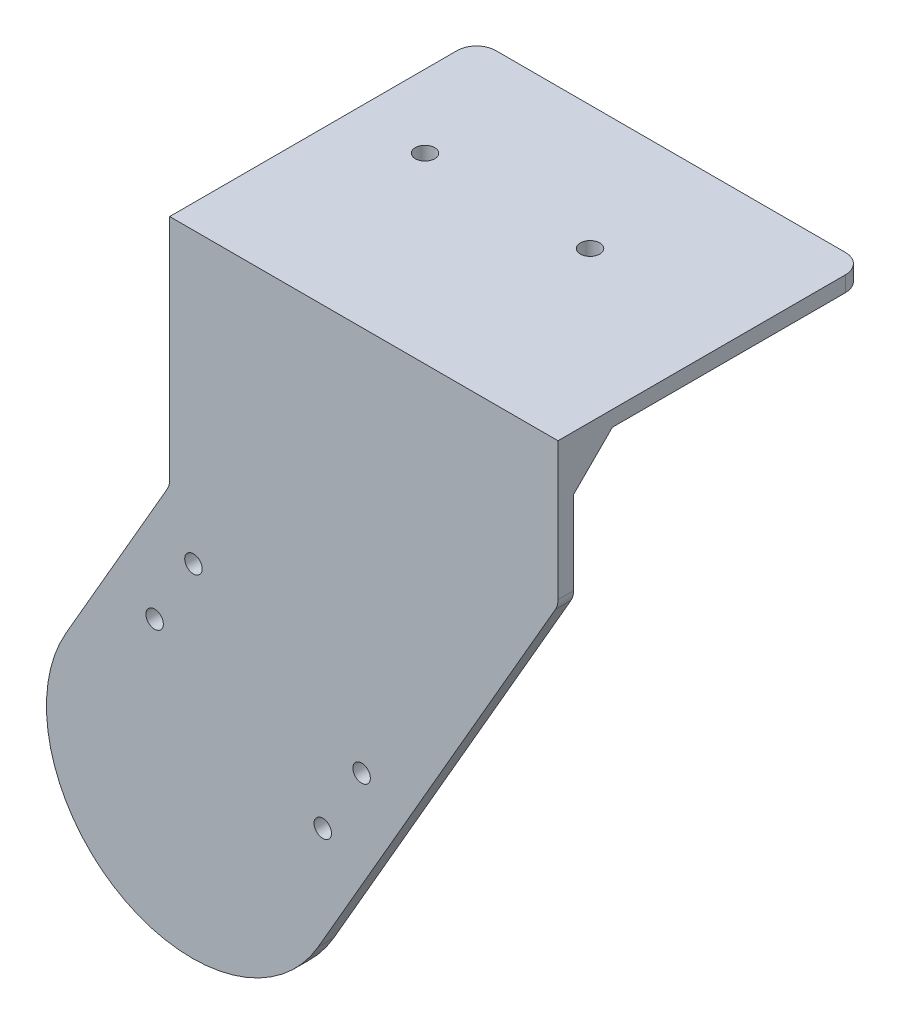
SolidWorks part; units mm, degrees
ref_plane "Front Plane" through (0, 0, 0) normal (0, 0, 1) x (1, 0, 0)
ref_plane "Top Plane" through (0, 0, 0) normal (0, 1, 0) x (1, 0, 0)
ref_plane "Right Plane" through (0, 0, 0) normal (1, 0, 0) x (0, 0, -1)
sketch "Sketch1" plane through (0, 0, 0) normal (0, 0, 1) x (1, 0, 0)
  line L0 (0, 0) -> (40.2373, 0) construction
  line L1 (64.9519, -37.5) -> (0, 0) construction
  line L2 (0, 0) -> (-64.9519, 37.5) construction
  line L3 (-64.9519, 37.5) -> (-11.547, 130)
  line L4 (64.9519, -37.5) -> (188.453, 176.4102)
  line L5 (-11.547, 130) -> (-11.547, 250)
  line L6 (-11.547, 250) -> (188.453, 250)
  line L7 (188.453, 250) -> (188.453, 176.4102)
  arc A0 (64.9519, -37.5) -> (-64.9519, 37.5) centre (0, 0) cw
  dimension "D2" = 75
  dimension "D1" = 30
  dimension "D4" = 130
  dimension "D5" = 200
  dimension "D6" = 120
extrude "Boss-Extrude1" add sketch "Sketch1" along normal blind 8
sketch "Sketch4" plane through (-11.547, 0, 0) normal (-1, 0, 0) x (0, 0, 1)
  line L5 (0, 242) -> (0, 250)
  line L6 (0, 250) -> (0, 130) construction
  line L7 (0, 250) -> (-150, 250)
  line L8 (0, 250) -> (0, 130)
  line L9 (0, 130) -> (8, 130)
  line L10 (8, 130) -> (8, 250)
  line L11 (8, 250) -> (0, 250)
  line L13 (0, 130) -> (8, 130)
  line L15 (-150, 250) -> (-150, 242)
  line L16 (-150, 242) -> (0, 242)
  dimension "D4" = 150
  dimension "D5" = 8
  dimension "D3" = 0
extrude "Boss-Extrude2" add sketch "Sketch4" along direction (-1, 0, 0) on the side against the normal up to surface (200 mm away)
chamfer "Chamfer1" distance 20 angle 45 1 edges at (88.453, 242, 0)
sketch "Sketch5" plane through (0, 250, 0) normal (0, 1, 0) x (1, 0, 0)
  line L0 (188.453, -8) -> (188.453, 150) construction
  line L2 (68.453, 86) -> (68.453, 76) construction
  line L3 (110.953, 86) -> (68.453, 86) construction
  line L4 (68.453, 86) -> (68.453, 150) construction
  line L5 (188.453, 150) -> (-11.547, 150) construction
  line L6 (68.453, 86) -> (25.953, 86) construction
  circle A0 centre (68.453, 86) radius 10 construction
  circle A1 centre (110.953, 86) radius 5
  circle A2 centre (25.953, 86) radius 5
  dimension "D3" = 20
  dimension "D4" = 10
  dimension "D1" = 120
  dimension "D2" = 64
  dimension "D5" = 85
extrude "Cut-Extrude1" cut sketch "Sketch5" against normal up to next
sketch "Sketch6" plane through (0, 0, 0) normal (0, 0, 1) x (1, 0, 0)
  line L0 (-32.9519, 92.9256) -> (96.9519, 17.9256) construction
  line L1 (-11.547, 130) -> (-64.9519, 37.5) construction
  line L2 (64.9519, -37.5) -> (188.453, 176.4102) construction
  line L3 (-32.9519, 92.9256) -> (-28.9519, 99.8538) construction
  line L4 (-28.9519, 99.8538) -> (100.9519, 24.8538) construction
  line L5 (100.9519, 24.8538) -> (96.9519, 17.9256) construction
  line L6 (87.3013, 51.2102) -> (67.3013, 16.5692) construction
  line L7 (67.3013, 16.5692) -> (-19.3013, 66.5692) construction
  line L8 (-19.3013, 66.5692) -> (0.6987, 101.2102) construction
  line L9 (0.6987, 101.2102) -> (87.3013, 51.2102) construction
  line L10 (87.3013, 51.2102) -> (108.9519, 38.7102) construction
  line L11 (64.9519, -37.5) -> (188.453, 176.4102) construction
  line L12 (0.6987, 101.2102) -> (-20.9519, 113.7102) construction
  line L13 (-11.547, 130) -> (-64.9519, 37.5) construction
  circle A0 centre (87.3013, 51.2102) radius 4.5
  circle A1 centre (67.3013, 16.5692) radius 4.5
  circle A2 centre (-19.3013, 66.5692) radius 4.5
  circle A3 centre (0.6987, 101.2102) radius 4.5
  dimension "D3" = 9
  dimension "D1" = 64
  dimension "D2" = 8
  dimension "D4" = 16
  dimension "D5" = 16
  dimension "D6" = 100
extrude "Cut-Extrude3" cut sketch "Sketch6" along normal up to next
fillet "Fillet1" radius 10 4 edges at (-11.547, 246, -150) (188.453, 246, -150) (188.453, 176.4102, 4) (-11.547, 130, 4)
